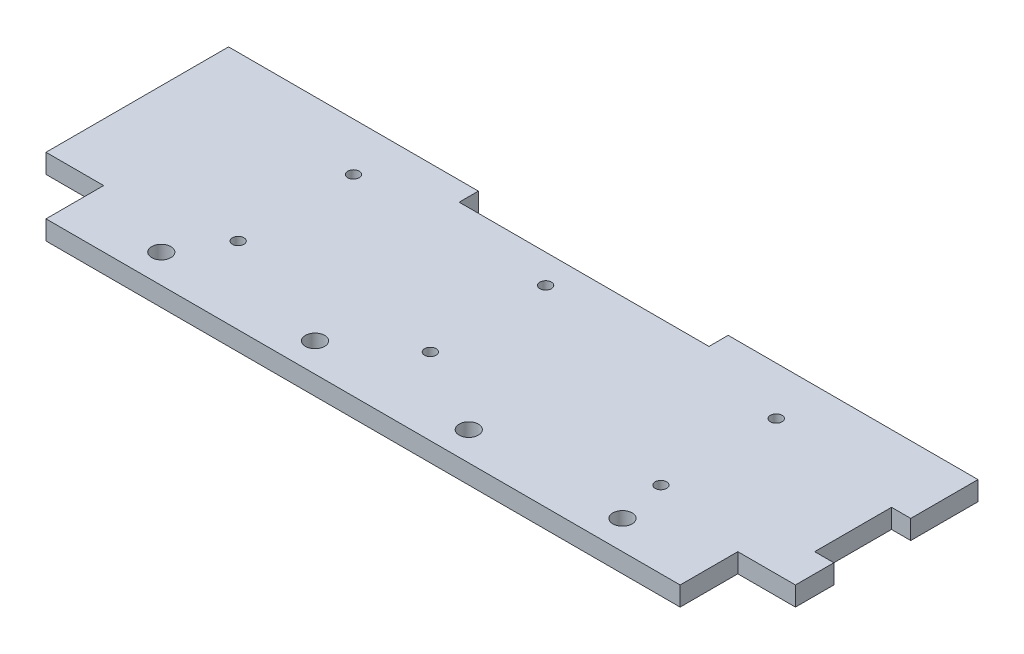
SolidWorks part; units mm, degrees
ref_plane "Front Plane" through (0, 0, 0) normal (0, 0, 1) x (1, 0, 0)
ref_plane "Top Plane" through (0, 0, 0) normal (0, 1, 0) x (1, 0, 0)
ref_plane "Right Plane" through (0, 0, 0) normal (1, 0, 0) x (0, 0, -1)
sketch "Sketch1" plane through (0, 0, 0) normal (0, 1, 0) x (1, 0, 0)
  line L36 (0, 15) -> (-390, 15)
  line L37 (-390, 15) -> (-390, 140)
  line L44 (0, 140) -> (-130, 140)
  line L45 (-130, 140) -> (-130, 130)
  line L46 (-130, 130) -> (-260, 130)
  line L47 (-260, 130) -> (-260, 140)
  line L48 (-260, 140) -> (-390, 140)
  line L49 (0, 140) -> (0, 105)
  line L50 (0, 105) -> (-10, 105)
  line L52 (0, 65) -> (0, 15)
  line L53 (-10, 105) -> (-10, 65)
  line L54 (-10, 65) -> (0, 65)
  circle A2 centre (-315, 30) radius 5
  circle A4 centre (-235, 30) radius 5
  circle A5 centre (-155, 30) radius 5
  circle A6 centre (-75, 30) radius 5
  circle A7 centre (-80, 55) radius 3
  circle A8 centre (-200, 55) radius 3
  circle A9 centre (-300, 55) radius 3
  circle A10 centre (-300, 115) radius 3
  circle A11 centre (-200, 115) radius 3
  circle A12 centre (-80, 115) radius 3
extrude "Boss-Extrude1" add sketch "Sketch1" along normal blind 10
sketch "Sketch2" plane through (0, 0, 0) normal (0, -1, 0) x (1, 0, 0)
  line L1 (0, -15) -> (-30, -15)
  line L2 (0, -15) -> (0, -45)
  line L3 (0, -45) -> (-30, -45)
  line L4 (-30, -15) -> (-30, -45)
  line L5 (-390, -15) -> (-360, -15)
  line L6 (-390, -15) -> (-390, -45)
  line L7 (-390, -45) -> (-360, -45)
  line L8 (-360, -15) -> (-360, -45)
extrude "Cut-Extrude1" cut sketch "Sketch2" against normal blind 10
